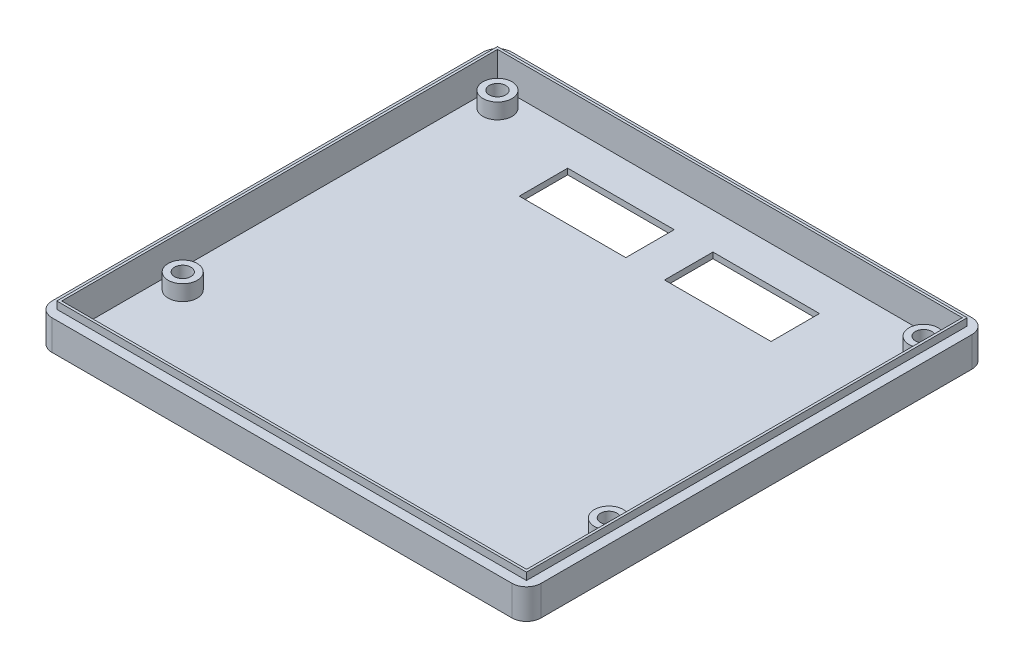
SolidWorks part; units mm, degrees
ref_plane "Front Plane" through (0, 0, 0) normal (0, 0, 1) x (1, 0, 0)
ref_plane "Top Plane" through (0, 0, 0) normal (0, 1, 0) x (1, 0, 0)
ref_plane "Right Plane" through (0, 0, 0) normal (1, 0, 0) x (0, 0, -1)
sketch "Sketch4" plane through (0, 0, 0) normal (0, 1, 0) x (1, 0, 0)
  line L0 (0, 0) -> (93, 0) construction
  line L1 (93, 0) -> (93, 87) construction
  line L2 (93, 87) -> (0, 87) construction
  line L3 (0, 87) -> (0, 0) construction
  dimension "D1" = 93
  dimension "D2" = 87
sketch "Sketch1" plane through (0, 0, 0) normal (0, 1, 0) x (1, 0, 0)
  line L8 (-4, -4) -> (97, -4)
  line L9 (97, -4) -> (97, 91)
  line L10 (-4, 91) -> (-4, -4)
  line L11 (97, 91) -> (-4, 91)
  line L12 (-4, -4) -> (97, -4)
  line L13 (97, -4) -> (97, 91)
  line L14 (-4, 91) -> (-4, -4)
  line L15 (97, 91) -> (-4, 91)
  dimension "D1" = 4
extrude "Boss-Extrude1" add sketch "Sketch1" along normal blind 1.2
sketch "Sketch3" plane through (0, 1.2, 0) normal (0, 1, 0) x (1, 0, 0)
  line L0 (-4, -4) -> (97, -4)
  line L1 (97, -4) -> (97, 91)
  line L2 (97, 91) -> (-4, 91)
  line L3 (-4, 91) -> (-4, -4)
  line L12 (-1.5, -1.5) -> (94.5, -1.5)
  line L13 (94.5, -1.5) -> (94.5, 88.5)
  line L14 (-1.5, 88.5) -> (-1.5, -1.5)
  line L15 (94.5, 88.5) -> (-1.5, 88.5)
  line L16 (-1.5, -1.5) -> (94.5, -1.5)
  line L17 (94.5, -1.5) -> (94.5, 88.5)
  line L18 (-1.5, 88.5) -> (-1.5, -1.5)
  line L19 (94.5, 88.5) -> (-1.5, 88.5)
  dimension "D1" = 1.5
extrude "Boss-Extrude2" add sketch "Sketch3" along normal blind 5
sketch "Sketch5" plane through (0, 1.2, 0) normal (0, 1, 0) x (1, 0, 0)
  line L0 (2.5, 84.5) -> (2.5, 87) construction
  line L1 (93, 87) -> (0, 87) construction
  line L2 (0, 84.5) -> (2.5, 84.5) construction
  line L3 (0, 87) -> (0, 0) construction
  line L4 (90.5, 84.5) -> (93, 84.5) construction
  line L5 (93, 0) -> (93, 87) construction
  circle A0 centre (2.5, 84.5) radius 3
  circle A1 centre (90.5, 84.5) radius 3
  circle A2 centre (90.5, 19.5) radius 3
  circle A3 centre (2.5, 19.5) radius 3
  dimension "D2" = 6
  dimension "D3" = 65
  dimension "D1" = 2.5
extrude "Boss-Extrude3" add sketch "Sketch5" along normal blind 3.2
sketch "Sketch6" plane through (0, 4.4, 0) normal (0, 1, 0) x (1, 0, 0)
  circle A0 centre (2.5, 84.5) radius 1.7
  circle A1 centre (90.5, 84.5) radius 1.7
  circle A2 centre (90.5, 19.5) radius 1.7
  circle A3 centre (2.5, 19.5) radius 1.7
  dimension "D1" = 3.4
extrude "Cut-Extrude1" cut sketch "Sketch6" against normal up to next
sketch "Sketch7" plane through (0, 1.2, 0) normal (0, 1, 0) x (1, 0, 0)
  line L0 (20.5, 81) -> (0, 81) construction
  line L1 (50.5, 71) -> (72.5, 71)
  line L2 (50.5, 71) -> (50.5, 81)
  line L3 (50.5, 81) -> (72.5, 81)
  line L4 (72.5, 71) -> (72.5, 81)
  line L5 (20.5, 71) -> (42.5, 71)
  line L6 (20.5, 71) -> (20.5, 81)
  line L7 (20.5, 81) -> (42.5, 81)
  line L8 (42.5, 71) -> (42.5, 81)
  line L9 (0, 87) -> (0, 0) construction
  line L10 (72.5, 81) -> (93, 81) construction
  line L11 (93, 0) -> (93, 87) construction
  line L13 (20.5, 76) -> (15.1095, 76) construction
  line L14 (93, 87) -> (0, 87) construction
  dimension "D1" = 8
  dimension "D2" = 22
  dimension "D3" = 52
  dimension "D4" = 10
  dimension "D5" = 11
extrude "Cut-Extrude2" cut sketch "Sketch7" against normal up to next
fillet "Fillet1" radius 3 4 edges at (97, 3.1, 4) (-4, 3.1, 4) (97, 3.1, -91) (-4, 3.1, -91)
sketch "Sketch8" plane through (0, 6.2, 0) normal (0, 1, 0) x (1, 0, 0)
  line L0 (-1.5, 88.5) -> (94.5, 88.5)
  line L1 (94.5, 88.5) -> (94.5, -1.5)
  line L2 (94.5, -1.5) -> (-1.5, -1.5)
  line L3 (-1.5, -1.5) -> (-1.5, 88.5)
  line L4 (-2, 89) -> (95, 89)
  line L5 (95, 89) -> (95, -2)
  line L6 (95, -2) -> (-2, -2)
  line L7 (-2, -2) -> (-2, 89)
  dimension "D1" = 0.5
extrude "Boss-Extrude4" add sketch "Sketch8" along normal blind 1.5
